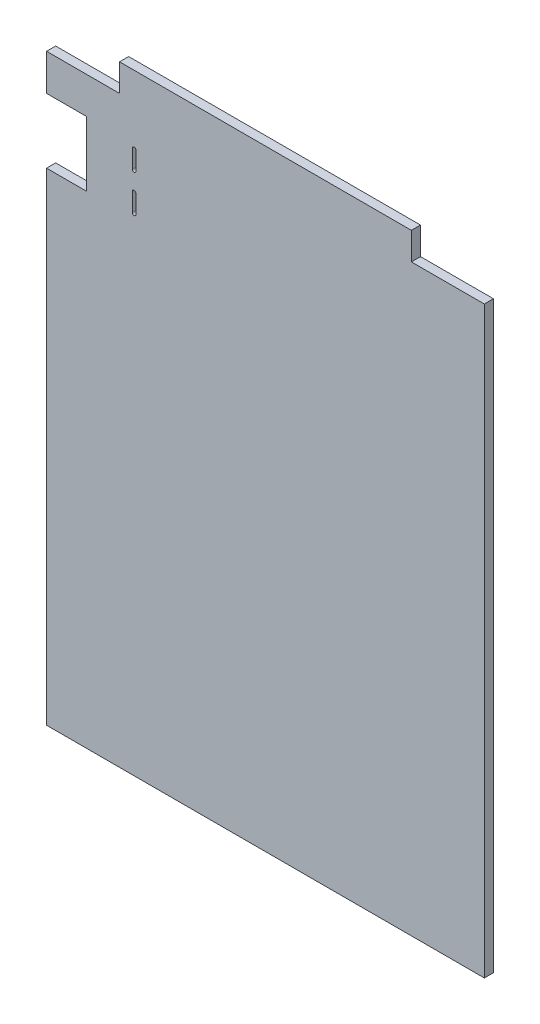
SolidWorks part; units mm, degrees
ref_plane "Plan de face" through (0, 0, 0) normal (0, 0, 1) x (1, 0, 0)
ref_plane "Plan de dessus" through (0, 0, 0) normal (0, 1, 0) x (1, 0, 0)
ref_plane "Plan de droite" through (0, 0, 0) normal (1, 0, 0) x (0, 0, -1)
sketch "Esquisse1" plane through (0, 0, 0) normal (0, 0, 1) x (1, 0, 0)
  line L1 (-290, 335) -> (190, 335)
  line L2 (-290, 335) -> (-290, -335)
  line L3 (-290, -335) -> (190, -335)
  line L4 (190, 335) -> (190, -335)
  dimension "D1" = 480
  dimension "D2" = 670
  dimension "D3" = 335
  dimension "D4" = 190
extrude "Boss.-Extru.1" add sketch "Esquisse1" along normal blind 10
sketch "Esquisse2" plane through (0, 0, 0) normal (0, 0, -1) x (-1, 0, 0)
  line L1 (-190, 335) -> (-110, 335)
  line L2 (-190, 335) -> (-190, 305)
  line L3 (-190, 305) -> (-110, 305)
  line L4 (-110, 335) -> (-110, 305)
  line L5 (290, 335) -> (210, 335)
  line L6 (290, 335) -> (290, 305)
  line L7 (290, 305) -> (210, 305)
  line L8 (210, 335) -> (210, 305)
  dimension "D1" = 30
  dimension "D2" = 30
  dimension "D3" = 80
  dimension "D4" = 80
extrude "Enlèv. mat.-Extru.1" cut sketch "Esquisse2" against normal through all
sketch "Esquisse3" plane through (0, 0, 0) normal (0, 0, -1) x (-1, 0, 0)
  line L0 (192, 260) -> (192, 240)
  line L1 (196, 260) -> (196, 240)
  line L2 (192, 219) -> (192, 199)
  line L3 (196, 199) -> (196, 219)
  line L4 (290, 305) -> (290, -335) construction
  line L5 (290, 265) -> (246, 265)
  line L6 (290, 265) -> (290, 194)
  line L7 (290, 194) -> (246, 194)
  line L8 (246, 265) -> (246, 194)
  line L9 (210, 305) -> (290, 305) construction
  arc A0 (196, 260) -> (192, 260) centre (194, 260) ccw
  arc A1 (196, 219) -> (192, 219) centre (194, 219) ccw
  arc A2 (192, 240) -> (196, 240) centre (194, 240) ccw
  arc A3 (192, 199) -> (196, 199) centre (194, 199) ccw
  dimension "D1" = 4
  dimension "D2" = 4
  dimension "D3" = 41
  dimension "D4" = 4
  dimension "D5" = 4
  dimension "D6" = 20
  dimension "D7" = 20
  dimension "D11" = 5
  dimension "D12" = 52
  dimension "D8" = 44
  dimension "D9" = 71
  dimension "D10" = 40
extrude "Enlèv. mat.-Extru.2" cut sketch "Esquisse3" against normal through all
